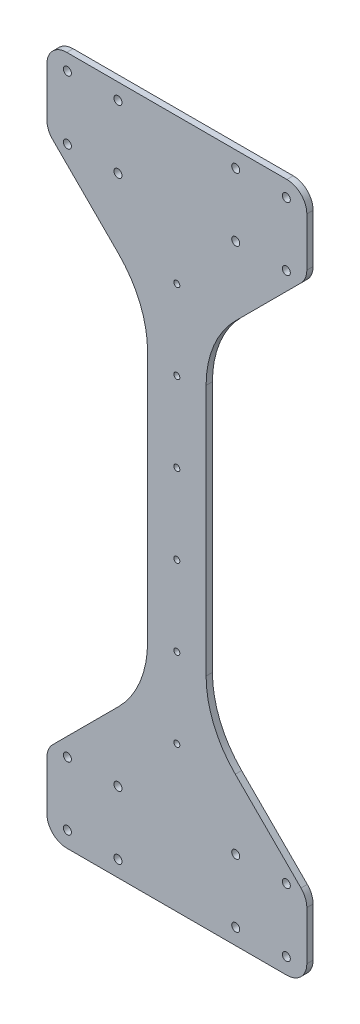
SolidWorks part; units mm, degrees
ref_plane "Front Plane" through (0, 0, 0) normal (0, 0, 1) x (1, 0, 0)
ref_plane "Top Plane" through (0, 0, 0) normal (0, 1, 0) x (1, 0, 0)
ref_plane "Right Plane" through (0, 0, 0) normal (1, 0, 0) x (0, 0, -1)
sketch "Sketch1" plane through (0, 0, 0) normal (0, 0, 1) x (1, 0, 0)
  line L0 (39.3854, -40.0501) -> (39.3854, -52.4111) construction
  line L1 (165.9345, -56.675) -> (165.9345, -42.05) construction
  line L2 (157.3152, -8.05) -> (165.9345, -16.6693)
  line L3 (157.3152, 245.3495) -> (165.9345, 253.9688)
  line L4 (39.3854, -40.0501) -> (39.3854, -52.4111)
  line L5 (165.9345, -56.675) -> (165.9345, -42.05)
  line L6 (165.9345, 245.3495) -> (39.3854, 245.3495)
  line L7 (165.9345, 279.3495) -> (165.9345, 245.3495)
  line L8 (39.3854, -52.4111) -> (165.9345, -56.675)
  line L9 (39.3854, 289.7105) -> (165.9345, 293.9745)
  line L10 (39.3854, -40.0501) -> (39.3854, -16.6693)
  line L11 (165.9345, -42.05) -> (165.9345, -16.6693)
  line L12 (157.3152, -8.05) -> (48.0047, -8.0501)
  line L13 (42.1433, 0) -> (42.1433, 237.2995) construction
  line L14 (42.1433, 118.6497) -> (215.0534, 118.6497) construction
  line L15 (165.9345, 293.9745) -> (165.9345, 279.3495)
  line L16 (39.3854, 277.3495) -> (39.3854, 245.3495)
  line L17 (39.3854, 277.3495) -> (39.3854, 289.7105)
  line L18 (102.66, -54.5431) -> (102.66, 291.8425) construction
  line L19 (102.66, 291.8425) -> (73.0854, -499321.8282) construction
  line L20 (39.3854, -16.6693) -> (89.96, 33.9052)
  line L21 (89.96, -8.05) -> (115.36, -8.05)
  line L22 (89.96, -8.05) -> (89.96, 245.3495)
  line L23 (89.96, 245.3495) -> (115.36, 245.3495)
  line L24 (115.36, -8.05) -> (115.36, 245.3495)
  line L25 (89.96, -8.05) -> (115.36, 245.3495) construction
  line L26 (89.96, 245.3495) -> (115.36, -8.05) construction
  line L27 (115.36, 33.9052) -> (157.3152, -8.05)
  line L28 (115.36, 203.3943) -> (157.3152, 245.3495)
  line L29 (39.3854, 253.9688) -> (89.96, 203.3943)
  arc A0 (157.6345, 249.9303) -> (157.6345, 253.9689) centre (157.6345, 251.9496) cw
  arc A1 (157.6345, 253.9689) -> (157.6345, 249.9303) centre (157.6345, 251.9496) cw
  arc A2 (73.0854, 249.9303) -> (73.0854, 253.9689) centre (73.0854, 251.9496) ccw
  arc A3 (73.0854, 253.9689) -> (73.0854, 249.9303) centre (73.0854, 251.9496) ccw
  arc A4 (73.0854, 249.9303) -> (73.0854, 253.9689) centre (73.0854, 251.9496) ccw
  arc A5 (73.0854, 253.9689) -> (73.0854, 249.9303) centre (73.0854, 251.9496) ccw
  arc A6 (47.6854, 249.9303) -> (47.6854, 253.9689) centre (47.6854, 251.9496) cw
  arc A7 (47.6854, 253.9689) -> (47.6854, 249.9303) centre (47.6854, 251.9496) cw
  arc A10 (47.6854, 281.6802) -> (47.6854, 285.7188) centre (47.6854, 283.6995) cw
  arc A11 (47.6854, 285.7188) -> (47.6854, 281.6802) centre (47.6854, 283.6995) cw
  arc A14 (157.6345, -48.4194) -> (157.6345, -44.3807) centre (157.6345, -46.4001) ccw
  arc A15 (157.6345, -44.3807) -> (157.6345, -48.4194) centre (157.6345, -46.4001) ccw
  arc A16 (157.6345, -48.4194) -> (157.6345, -44.3807) centre (157.6345, -46.4001) ccw
  arc A17 (157.6345, -44.3807) -> (157.6345, -48.4194) centre (157.6345, -46.4001) ccw
  arc A18 (73.0854, 281.6802) -> (73.0854, 285.7188) centre (73.0854, 283.6995) cw
  arc A19 (73.0854, 285.7188) -> (73.0854, 281.6802) centre (73.0854, 283.6995) cw
  arc A22 (157.6345, -16.6693) -> (157.6345, -12.6307) centre (157.6345, -14.65) ccw
  arc A23 (157.6345, -12.6307) -> (157.6345, -16.6693) centre (157.6345, -14.65) ccw
  arc A24 (157.6345, -16.6693) -> (157.6345, -12.6307) centre (157.6345, -14.65) ccw
  arc A25 (157.6345, -12.6307) -> (157.6345, -16.6693) centre (157.6345, -14.65) ccw
  arc A26 (73.0854, -16.6693) -> (73.0854, -12.6307) centre (73.0854, -14.65) ccw
  arc A27 (73.0854, -12.6307) -> (73.0854, -16.6693) centre (73.0854, -14.65) ccw
  arc A28 (73.0854, -16.6693) -> (73.0854, -12.6307) centre (73.0854, -14.65) ccw
  arc A29 (73.0854, -12.6307) -> (73.0854, -16.6693) centre (73.0854, -14.65) ccw
  arc A30 (73.0854, 249.9303) -> (73.0854, 253.9689) centre (73.0854, 251.9496) cw
  arc A31 (73.0854, 253.9689) -> (73.0854, 249.9303) centre (73.0854, 251.9496) cw
  arc A34 (157.6345, 249.9303) -> (157.6345, 253.9689) centre (157.6345, 251.9496) ccw
  arc A35 (157.6345, 253.9689) -> (157.6345, 249.9303) centre (157.6345, 251.9496) ccw
  arc A36 (157.6345, 249.9303) -> (157.6345, 253.9689) centre (157.6345, 251.9496) ccw
  arc A37 (157.6345, 253.9689) -> (157.6345, 249.9303) centre (157.6345, 251.9496) ccw
  arc A38 (47.6854, 249.9303) -> (47.6854, 253.9689) centre (47.6854, 251.9496) ccw
  arc A39 (47.6854, 253.9689) -> (47.6854, 249.9303) centre (47.6854, 251.9496) ccw
  arc A40 (47.6854, 249.9303) -> (47.6854, 253.9689) centre (47.6854, 251.9496) ccw
  arc A41 (47.6854, 253.9689) -> (47.6854, 249.9303) centre (47.6854, 251.9496) ccw
  arc A42 (73.0854, -48.4194) -> (73.0854, -44.3807) centre (73.0854, -46.4001) ccw
  arc A43 (73.0854, -44.3807) -> (73.0854, -48.4194) centre (73.0854, -46.4001) ccw
  arc A44 (73.0854, -48.4194) -> (73.0854, -44.3807) centre (73.0854, -46.4001) ccw
  arc A45 (73.0854, -44.3807) -> (73.0854, -48.4194) centre (73.0854, -46.4001) ccw
  arc A46 (132.2345, 249.9303) -> (132.2345, 253.9689) centre (132.2345, 251.9496) ccw
  arc A47 (132.2345, 253.9689) -> (132.2345, 249.9303) centre (132.2345, 251.9496) ccw
  arc A48 (132.2345, 249.9303) -> (132.2345, 253.9689) centre (132.2345, 251.9496) ccw
  arc A49 (132.2345, 253.9689) -> (132.2345, 249.9303) centre (132.2345, 251.9496) ccw
  arc A50 (47.6854, -48.4194) -> (47.6854, -44.3808) centre (47.6854, -46.4001) ccw
  arc A51 (47.6854, -44.3808) -> (47.6854, -48.4194) centre (47.6854, -46.4001) ccw
  arc A52 (47.6854, -48.4194) -> (47.6854, -44.3808) centre (47.6854, -46.4001) ccw
  arc A53 (47.6854, -44.3808) -> (47.6854, -48.4194) centre (47.6854, -46.4001) ccw
  arc A54 (47.6854, -16.6693) -> (47.6854, -12.6307) centre (47.6854, -14.65) ccw
  arc A55 (47.6854, -12.6307) -> (47.6854, -16.6693) centre (47.6854, -14.65) ccw
  arc A56 (47.6854, -16.6693) -> (47.6854, -12.6307) centre (47.6854, -14.65) ccw
  arc A57 (47.6854, -12.6307) -> (47.6854, -16.6693) centre (47.6854, -14.65) ccw
  arc A58 (157.6345, 281.6802) -> (157.6345, 285.7188) centre (157.6345, 283.6995) cw
  arc A59 (157.6345, 285.7188) -> (157.6345, 281.6802) centre (157.6345, 283.6995) cw
  arc A62 (132.2345, -16.6693) -> (132.2345, -12.6307) centre (132.2345, -14.65) ccw
  arc A63 (132.2345, -12.6307) -> (132.2345, -16.6693) centre (132.2345, -14.65) ccw
  arc A64 (132.2345, -16.6693) -> (132.2345, -12.6307) centre (132.2345, -14.65) ccw
  arc A65 (132.2345, -12.6307) -> (132.2345, -16.6693) centre (132.2345, -14.65) ccw
  arc A66 (132.2345, -48.4194) -> (132.2345, -44.3808) centre (132.2345, -46.4001) ccw
  arc A67 (132.2345, -44.3808) -> (132.2345, -48.4194) centre (132.2345, -46.4001) ccw
  arc A68 (132.2345, -48.4194) -> (132.2345, -44.3808) centre (132.2345, -46.4001) ccw
  arc A69 (132.2345, -44.3808) -> (132.2345, -48.4194) centre (132.2345, -46.4001) ccw
  point P62 (102.66, 118.6497)
  dimension "D3" = 0
  dimension "D2" = 25.4
  dimension "D1" = 0
  dimension "D4" = 0
  dimension "D5" = 0
  dimension "D6" = 0
  dimension "D7" = 0
  dimension "D9" = 0
  dimension "D10" = 0
  dimension "D11" = 0
  dimension "D12" = 0
  dimension "D13" = 0
  dimension "D14" = 0
extrude "Boss-Extrude1" add sketch "Sketch1" along normal blind 3.175 contours L20 L10 L4 L8 L5 L11 L2 L12 A69 A68 A65 A64 A57 A56 A53 A52 A45 A44 A29 A28 A25 A24 A17 A16 | L27 L24 L12 | L12 L24 L6 L22 | L12 L22 L20 | L16 L29 L6 L3 L7 L15 L9 L17 A49 A48 A5 A4 A0 A1 A6 A7 A10 A11 A18 A19 A58 A59 | L24 L28 L6 | L6 L29 L22
sketch "Sketch2" plane through (0, 0, 3.175) normal (0, 0, 1) x (1, 0, 0)
  line L0 (165.9345, -56.675) -> (165.9345, -16.6693) construction
  line L1 (39.3854, -52.4111) -> (84.3854, -52.4111)
  line L2 (39.3854, -52.4111) -> (39.3854, -7.4111)
  line L3 (39.3854, -7.4111) -> (84.3854, -7.4111)
  line L4 (84.3854, -52.4111) -> (84.3854, -7.4111)
  line L5 (165.9345, -52.4111) -> (120.9345, -52.4111)
  line L6 (165.9345, -52.4111) -> (165.9345, -7.4111)
  line L7 (165.9345, -7.4111) -> (120.9345, -7.4111)
  line L8 (120.9345, -52.4111) -> (120.9345, -7.4111)
  line L9 (89.96, 118.6497) -> (115.36, 118.6497) construction
  line L10 (89.96, 33.9052) -> (89.96, 203.3943) construction
  line L11 (115.36, 33.9052) -> (115.36, 203.3943) construction
  line L12 (165.9345, 289.7105) -> (120.9345, 289.7105)
  line L13 (39.3854, 289.7105) -> (84.3854, 289.7105)
  line L14 (84.3854, -52.4111) -> (120.9345, -52.4111)
  line L15 (84.3854, 289.7105) -> (120.9345, 289.7105)
  line M9 (39.3854, -52.4111) -> (165.9345, -56.675)
  line M10 (165.9345, -56.675) -> (165.9345, -16.6693)
  line M14 (165.9345, 253.9688) -> (165.9345, 293.9745)
  line M15 (165.9345, 293.9745) -> (39.3854, 289.7105)
  dimension "D1" = 45
extrude "Cut-Extrude1" cut sketch "Sketch2" against normal blind 10 contours L14 L1 L5 M9 M10 | L13 L15 L12 M14 M15
sketch "Sketch3" plane through (0, 0, 3.175) normal (0, 0, 1) x (1, 0, 0)
  line L25 (37.3854, -15.8409) -> (37.3854, -54.4111)
  line L26 (37.3854, -54.4111) -> (167.9345, -54.4111)
  line L27 (167.9345, -54.4111) -> (167.9345, -15.8409)
  line L28 (167.9345, -15.8409) -> (117.36, 34.7337)
  line L29 (117.36, 34.7337) -> (117.36, 202.5658)
  line L30 (117.36, 202.5658) -> (167.9345, 253.1404)
  line L31 (167.9345, 253.1404) -> (167.9345, 291.7105)
  line L32 (167.9345, 291.7105) -> (37.3854, 291.7105)
  line L33 (37.3854, 291.7105) -> (37.3854, 253.1404)
  line L34 (37.3854, 253.1404) -> (87.96, 202.5658)
  line L35 (87.96, 202.5658) -> (87.96, 34.7337)
  line L36 (87.96, 34.7337) -> (37.3854, -15.8409)
  line L37 (37.3854, -15.8409) -> (37.3854, -54.4111)
  line L38 (37.3854, -54.4111) -> (167.9345, -54.4111)
  line L39 (167.9345, -54.4111) -> (167.9345, -15.8409)
  line L40 (167.9345, -15.8409) -> (117.36, 34.7337)
  line L41 (117.36, 34.7337) -> (117.36, 202.5658)
  line L42 (117.36, 202.5658) -> (167.9345, 253.1404)
  line L43 (167.9345, 253.1404) -> (167.9345, 291.7105)
  line L44 (167.9345, 291.7105) -> (37.3854, 291.7105)
  line L45 (37.3854, 291.7105) -> (37.3854, 253.1404)
  line L46 (37.3854, 253.1404) -> (87.96, 202.5658)
  line L47 (87.96, 202.5658) -> (87.96, 34.7337)
  line L48 (87.96, 34.7337) -> (37.3854, -15.8409)
  circle A1 centre (132.2345, -46.4001) radius 2.0193
  circle A2 centre (132.2345, -46.4001) radius 2.0193
  circle A3 centre (132.2345, -14.65) radius 2.0193
  circle A4 centre (132.2345, -14.65) radius 2.0193
  circle A5 centre (47.6854, -14.65) radius 2.0193
  circle A6 centre (47.6854, -14.65) radius 2.0193
  circle A7 centre (47.6854, -46.4001) radius 2.0193
  circle A8 centre (47.6854, -46.4001) radius 2.0193
  circle A9 centre (73.0854, -46.4001) radius 2.0193
  circle A10 centre (73.0854, -46.4001) radius 2.0193
  circle A11 centre (73.0854, -14.65) radius 2.0193
  circle A12 centre (73.0854, -14.65) radius 2.0193
  circle A13 centre (157.6345, -14.65) radius 2.0193
  circle A14 centre (157.6345, -14.65) radius 2.0193
  circle A15 centre (157.6345, -46.4001) radius 2.0193
  circle A16 centre (157.6345, -46.4001) radius 2.0193
  circle A17 centre (132.2345, 251.9496) radius 2.0193
  circle A18 centre (132.2345, 251.9496) radius 2.0193
  circle A19 centre (73.0854, 251.9496) radius 2.0193
  circle A20 centre (73.0854, 251.9496) radius 2.0193
  circle A21 centre (157.6345, 251.9496) radius 2.0193
  circle A22 centre (157.6345, 251.9496) radius 2.0193
  circle A23 centre (47.6854, 251.9496) radius 2.0193
  circle A24 centre (47.6854, 251.9496) radius 2.0193
  circle A25 centre (47.6854, 283.6995) radius 2.0193
  circle A26 centre (47.6854, 283.6995) radius 2.0193
  circle A27 centre (73.0854, 283.6995) radius 2.0193
  circle A28 centre (73.0854, 283.6995) radius 2.0193
  circle A29 centre (157.6345, 283.6995) radius 2.0193
  circle A30 centre (157.6345, 283.6995) radius 2.0193
  dimension "D1" = 2
  dimension "D2" = 0
  dimension "D3" = 0
  dimension "D4" = 0
  dimension "D5" = 0
  dimension "D6" = 0
  dimension "D7" = 0
  dimension "D8" = 0
  dimension "D9" = 0
  dimension "D10" = 0
  dimension "D11" = 0
  dimension "D12" = 0
  dimension "D13" = 0
  dimension "D14" = 0
  dimension "D15" = 0
  dimension "D16" = 0
extrude "Boss-Extrude2" add sketch "Sketch3" against normal up to surface (3.175 mm away) up to face at (159.6538, 283.6995, 0)
fillet "Fillet1" radius 10 8 edges at (37.3854, 253.1404, 1.5875) (37.3854, 291.7105, 1.5875) (167.9345, 291.7105, 1.5875) (167.9345, 253.1404, 1.5875) (37.3854, -15.8409, 1.5875) (167.9345, -15.8409, 1.5875) (167.9345, -54.4111, 1.5875) (37.3854, -54.4111, 1.5875)
fillet "Fillet2" radius 50 4 edges at (87.96, 34.7337, 1.5875) (117.36, 34.7337, 1.5875) (87.96, 202.5658, 1.5875) (117.36, 202.5658, 1.5875)
sketch "Sketch4" plane through (0, 0, 3.175) normal (0, 0, 1) x (1, 0, 0)
  circle A0 centre (132.2345, 283.6995) radius 2.02
  dimension "D1" = 4.04
extrude "Cut-Extrude2" cut sketch "Sketch4" against normal blind 10
sketch "Sketch5" plane through (0, 0, 0) normal (0, 0, -1) x (-1, 0, 0)
  line L0 (-117.36, 118.6497) -> (-87.96, 118.6497) construction
  line L1 (-117.36, 181.8552) -> (-117.36, 55.4443) construction
  line L2 (-87.96, 55.4443) -> (-87.96, 181.8552) construction
  line L3 (-102.66, 118.6497) -> (-102.66, 31.7159) construction
  circle A0 centre (-102.66, 58.6497) radius 1.5
  circle A1 centre (-102.66, 98.6497) radius 1.5
  circle A2 centre (-102.66, 138.6497) radius 1.5
  circle A3 centre (-102.66, 178.6497) radius 1.5
  circle A4 centre (-102.66, 18.6497) radius 1.5
  circle A5 centre (-102.66, 218.6497) radius 1.5
  dimension "D1" = 3
  dimension "D2" = 3
  dimension "D5" = 3
  dimension "D6" = 3
  dimension "D3" = 40
  dimension "D4" = 20
  dimension "D7" = 40
  dimension "D8" = 40
extrude "Cut-Extrude3" cut sketch "Sketch5" against normal blind 10
